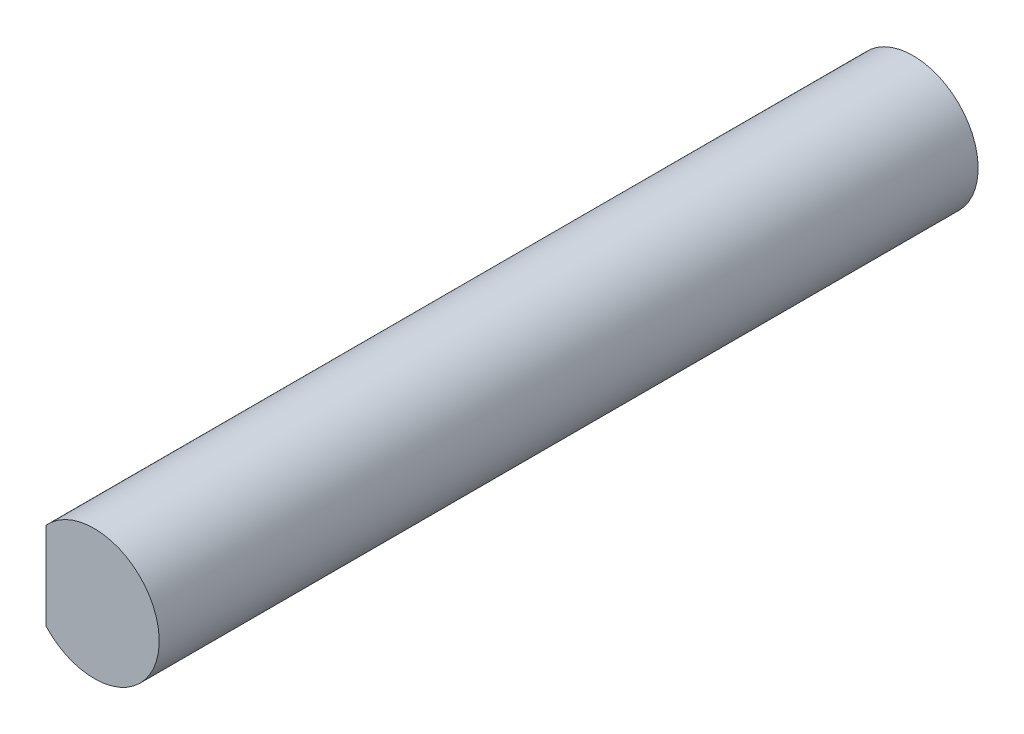
SolidWorks part; units mm, degrees
ref_plane "Front Plane" through (0, 0, 0) normal (0, 0, 1) x (1, 0, 0)
ref_plane "Top Plane" through (0, 0, 0) normal (0, 1, 0) x (1, 0, 0)
ref_plane "Right Plane" through (0, 0, 0) normal (1, 0, 0) x (0, 0, -1)
sketch "Sketch2" plane through (0, 0, 0) normal (0, 0, 1) x (1, 0, 0)
  circle A0 centre (0, 0) radius 1.35
  dimension "D1" = 2.7
extrude "Boss-Extrude1" add sketch "Sketch2" along normal mid plane 17
sketch "Sketch4" plane through (0, 0, -8.5) normal (0, 0, -1) x (-1, 0, 0)
  line L0 (1, 0.9069) -> (1, -0.9069)
  arc A0 (1, -0.9069) -> (1, 0.9069) centre (0, 0) ccw
  dimension "D2" = 2.7
  dimension "D1" = 1
extrude "Cut-Extrude1" cut sketch "Sketch4" against normal blind 6.4
sketch "Sketch5" plane through (0, 0, 8.5) normal (0, 0, 1) x (1, 0, 0)
  line L0 (-1, 0.9069) -> (-1, -0.9069)
  arc A0 (-1, 0.9069) -> (-1, -0.9069) centre (0, 0) ccw
  dimension "D2" = 1.35
  dimension "D1" = 1
extrude "Cut-Extrude2" cut sketch "Sketch5" against normal blind 3.2
